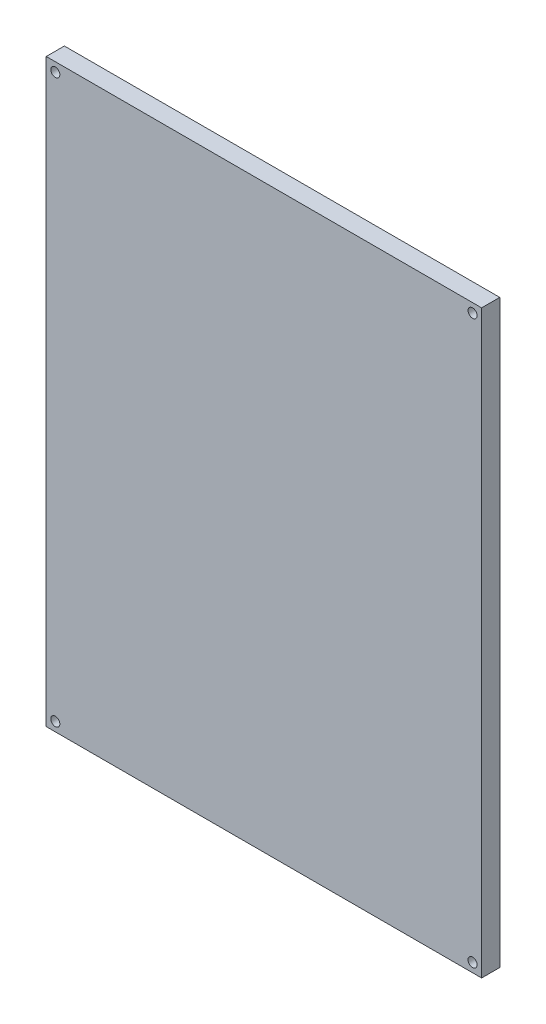
SolidWorks part; units mm, degrees
ref_plane "Front Plane" through (0, 0, 0) normal (0, 0, 1) x (1, 0, 0)
ref_plane "Top Plane" through (0, 0, 0) normal (0, 1, 0) x (1, 0, 0)
ref_plane "Right Plane" through (0, 0, 0) normal (1, 0, 0) x (0, 0, -1)
sketch "Sketch1" plane through (0, 0, 0) normal (0, 0, 1) x (1, 0, 0)
  line L0 (0, 160.065) -> (0, -160.065) construction
  line L1 (-120.075, 0) -> (120.075, 0) construction
  line L2 (-120.075, 160.065) -> (120.075, 160.065)
  line L3 (120.075, 160.065) -> (120.075, -160.065)
  line L4 (120.075, -160.065) -> (-120.075, -160.065)
  line L5 (-120.075, -160.065) -> (-120.075, 160.065)
  circle A0 centre (-115.075, 155.065) radius 2.5
  circle A1 centre (115.075, 155.065) radius 2.5
  circle A2 centre (-115.075, -155.065) radius 2.5
  circle A3 centre (115.075, -155.065) radius 2.5
  dimension "D3" = 5
  dimension "D4" = 5
  dimension "D5" = 5
  dimension "D6" = 5
  dimension "D7" = 5
  dimension "D8" = 5
  dimension "D9" = 5
  dimension "D10" = 5
  dimension "D11" = 5
  dimension "D12" = 5
  dimension "D13" = 5
  dimension "D14" = 5
  dimension "D1" = 240.15
  dimension "D2" = 320.13
extrude "Boss-Extrude1" add sketch "Sketch1" along normal blind 10
